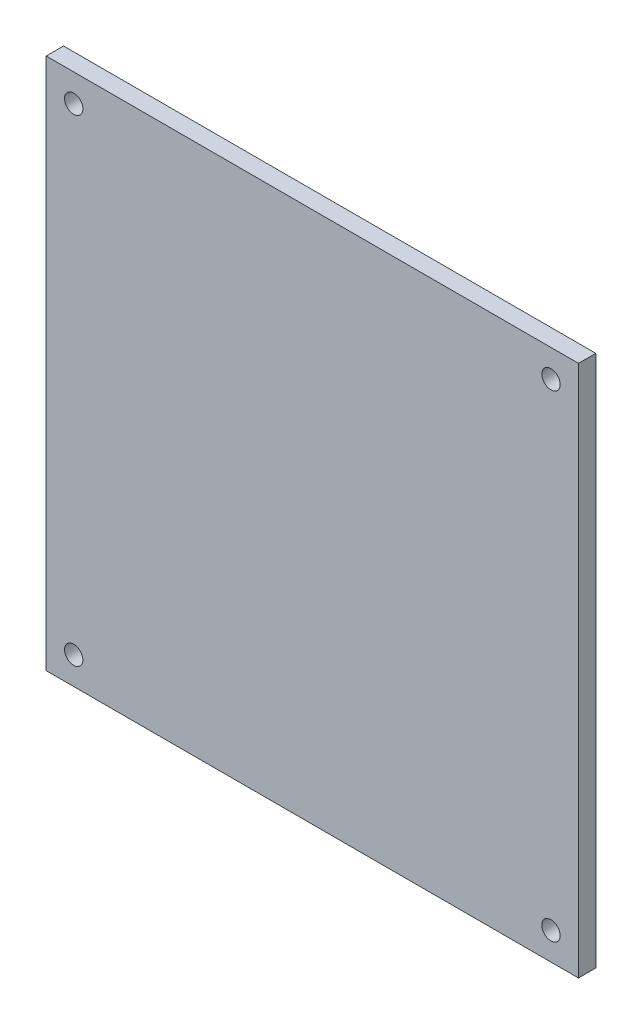
SolidWorks part; units mm, degrees
ref_plane "Front Plane" through (0, 0, 0) normal (0, 0, 1) x (1, 0, 0)
ref_plane "Top Plane" through (0, 0, 0) normal (0, 1, 0) x (1, 0, 0)
ref_plane "Right Plane" through (0, 0, 0) normal (1, 0, 0) x (0, 0, -1)
sketch "Sketch1" plane through (0, 0, 0) normal (0, 0, 1) x (1, 0, 0)
  line L0 (92.075, 184.15) -> (92.075, 0) construction
  line L1 (0, 0) -> (184.15, 0)
  line L2 (0, 0) -> (0, 184.15)
  line L3 (0, 184.15) -> (184.15, 184.15)
  line L4 (184.15, 0) -> (184.15, 184.15)
  line L5 (0, 92.075) -> (184.15, 92.075) construction
  circle A0 centre (9.525, 174.625) radius 3.175
  circle A1 centre (9.525, 9.525) radius 3.175
  circle A2 centre (174.625, 174.625) radius 3.175
  circle A3 centre (174.625, 9.525) radius 3.175
  dimension "D3" = 6.35
  dimension "D5" = 82.55
  dimension "D1" = 184.15
  dimension "D2" = 184.15
  dimension "D4" = 165.1
  dimension "D6" = 165.1
  dimension "D7" = 82.55
extrude "Boss-Extrude1" add sketch "Sketch1" along normal blind 5.9944
